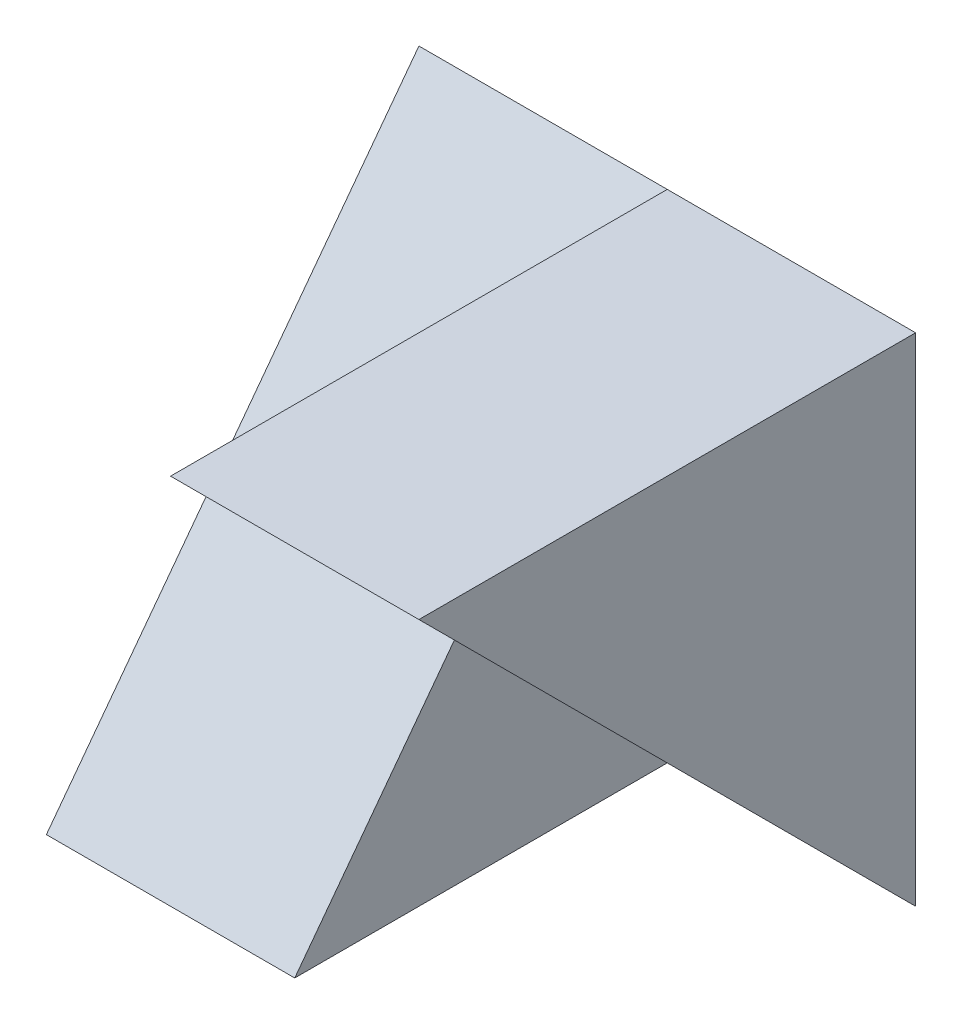
SolidWorks part; units mm, degrees
ref_plane "Front Plane" through (0, 0, 0) normal (0, 0, 1) x (1, 0, 0)
ref_plane "Top Plane" through (0, 0, 0) normal (0, 1, 0) x (1, 0, 0)
ref_plane "Right Plane" through (0, 0, 0) normal (1, 0, 0) x (0, 0, -1)
sketch "Sketch1" plane through (0, 0, 0) normal (1, 0, 0) x (0, 0, -1)
  line L1 (0, 0) -> (4, 0)
  line L2 (0, 0) -> (0, 4)
  line L3 (0, 4) -> (4, 4)
  line L4 (4, 0) -> (4, 4)
  dimension "D1" = 4
  dimension "D2" = 4
extrude "Boss-Extrude1" add sketch "Sketch1" along normal blind 2
sketch "Sketch2" plane through (0, 0, 0) normal (-1, 0, 0) x (0, 0, 1)
  line L0 (-1, 0) -> (-1, 4)
  line L1 (0, 0) -> (-4, 0) construction
  line L2 (-4, 0) -> (-4, 4) construction
  line L3 (-4, 4) -> (-4, 0)
  line L4 (-4, 0) -> (-1, 0)
  line L5 (-4, 4) -> (0, 4) construction
  line L6 (-1, 4) -> (-4, 4)
  dimension "D1" = 3
  dimension "D2" = 4
extrude "Boss-Extrude2" add sketch "Sketch2" along normal blind 2
sketch "Sketch3" plane through (2, 0, 0) normal (1, 0, 0) x (0, 0, -1)
  line L0 (4, 0) -> (0, 4)
  line L1 (0, 4) -> (0, 0) construction
  line L2 (0, 4) -> (4, 4)
  line L3 (4, 4) -> (4, 0)
  line M4 (0, 4) -> (0, 0)
  line M5 (0, 0) -> (4, 0)
extrude "Cut-Extrude1" cut sketch "Sketch3" against normal blind 2 contours L0 M5 M4
sketch "Sketch4" plane through (-2, 0, 0) normal (-1, 0, 0) x (0, 0, 1)
  line L0 (-1, 0) -> (-4, 4)
  line L1 (-4, 4) -> (-1, 4)
  line L2 (-1, 4) -> (-1, 0)
extrude "Cut-Extrude2" cut sketch "Sketch4" against normal blind 2
